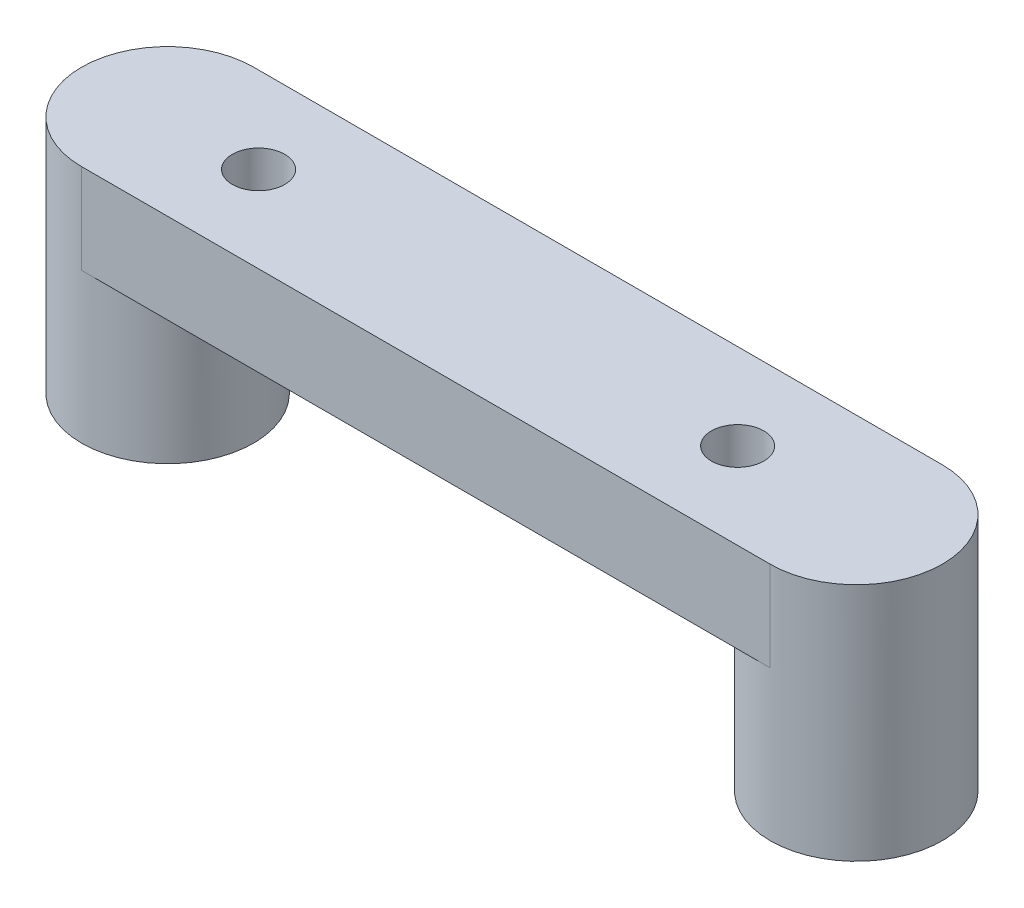
SolidWorks part; units mm, degrees
material "PET"
ref_plane "Front Plane" through (0, 0, 0) normal (0, 0, 1) x (1, 0, 0)
ref_plane "Top Plane" through (0, 0, 0) normal (0, 1, 0) x (1, 0, 0)
ref_plane "Right Plane" through (0, 0, 0) normal (1, 0, 0) x (0, 0, -1)
sketch "Sketch1" plane through (0, 0, 0) normal (0, 1, 0) x (1, 0, 0)
  line L0 (11.5, 0) -> (-11.5, 0)
  circle A0 centre (-11.5, 0) radius 0.875
  circle A1 centre (11.5, 0) radius 0.875
  circle A2 centre (-11.5, 0) radius 2.875
  circle A3 centre (11.5, 0) radius 2.875
  point P8 (0, 0)
  dimension "D1" = 1.75
  dimension "D2" = 1.75
  dimension "D3" = 23
  dimension "D4" = 2
extrude "Boss-Extrude1" add sketch "Sketch1" along normal blind 5
sketch "Sketch2" plane through (0, 5, 0) normal (0, 1, 0) x (1, 0, 0)
  line L1 (-11.5, 2.875) -> (11.5, 2.875)
  line L2 (-11.5, 2.875) -> (-11.5, -2.875)
  line L3 (-11.5, -2.875) -> (11.5, -2.875)
  line L4 (11.5, 2.875) -> (11.5, -2.875)
  circle A0 centre (-11.5, 0) radius 2.875 construction
  circle A1 centre (11.5, 0) radius 2.875 construction
  circle A2 centre (-11.5, 0) radius 2.875
  circle A3 centre (11.5, 0) radius 2.875
  circle M1 centre (-11.5, 0) radius 0.875
  circle M2 centre (-11.5, 0) radius 2.875
extrude "Boss-Extrude2" add sketch "Sketch2" along normal blind 3 contours L2 M1 | L2 M1 | L2 M2 M1 | L2 M2 M1 | A3 L1 L3 M2 | L4 A3 | L4 A3
sketch "Sketch3" plane through (0, 8, 0) normal (0, 1, 0) x (1, 0, 0)
  circle A3 centre (-8.4627, 0) radius 0.875
  circle A4 centre (7.5372, 0) radius 0.875
  point P4 (0, 0)
  point P5 (0, 0)
  dimension "D2" = 1.75
  dimension "D3" = 1.75
  dimension "D1" = 15.9999
extrude "Cut-Extrude1" cut sketch "Sketch3" against normal up to surface (3 mm away) up to face at (0, 5, 0)
equation "\"D2@Sketch1\"=\"D1@Sketch1\""
equation "\"D3@Sketch3\"=\"D2@Sketch3\""
